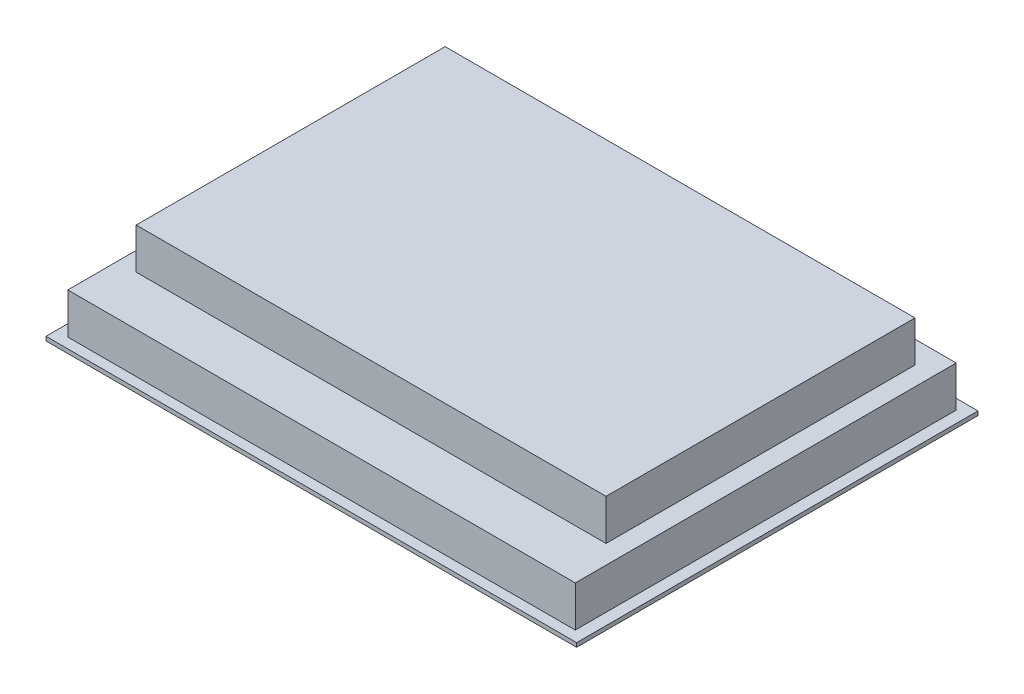
SolidWorks part; units mm, degrees
ref_plane "前视基准面" through (0, 0, 0) normal (0, 0, 1) x (1, 0, 0)
ref_plane "上视基准面" through (0, 0, 0) normal (0, 1, 0) x (1, 0, 0)
ref_plane "右视基准面" through (0, 0, 0) normal (1, 0, 0) x (0, 0, -1)
sketch "草图1" plane through (0, 0, 0) normal (0, 1, 0) x (1, 0, 0)
  line L1 (-195, -147.5) -> (195, -147.5)
  line L2 (-195, -147.5) -> (-195, 147.5)
  line L3 (-195, 147.5) -> (195, 147.5)
  line L4 (195, -147.5) -> (195, 147.5)
  line L5 (-195, -147.5) -> (195, 147.5) construction
  line L6 (-195, 147.5) -> (195, -147.5) construction
  point P0 (0, 0)
extrude "拉伸1" add sketch "草图1" along normal blind 3
sketch "草图2" plane through (0, 3, 0) normal (0, 1, 0) x (1, 0, 0)
  line L1 (-186.5, 140) -> (186.5, 140)
  line L2 (-186.5, 140) -> (-186.5, -140)
  line L3 (-186.5, -140) -> (186.5, -140)
  line L4 (186.5, 140) -> (186.5, -140)
  line L5 (-186.5, 140) -> (186.5, -140) construction
  line L6 (-186.5, -140) -> (186.5, 140) construction
  line L11 (-167.4114, -85.6768) -> (167.4114, 121.4193) construction
  line L12 (-167.4114, 121.4193) -> (167.4114, -85.6768) construction
  point P0 (0, 0)
  point P6 (0, 17.8712)
extrude "拉伸2" add sketch "草图2" along normal blind 30
sketch "草图4" plane through (0, 33, 0) normal (0, 1, 0) x (1, 0, 0)
  line L1 (-172.6676, 123.5217) -> (172.6676, 123.5217)
  line L2 (-172.6676, 123.5217) -> (-172.6676, -103.548)
  line L3 (-172.6676, -103.548) -> (172.6676, -103.548)
  line L4 (172.6676, 123.5217) -> (172.6676, -103.548)
  line L5 (-172.6676, 123.5217) -> (172.6676, -103.548) construction
  line L6 (-172.6676, -103.548) -> (172.6676, 123.5217) construction
  point P0 (0, 9.9869)
extrude "拉伸3" add sketch "草图4" along normal blind 30
sketch "草图5" plane through (0, 0, 0) normal (0, -1, 0) x (1, 0, 0)
  line L1 (195, 147.5) -> (195, -147.5) construction
  line L2 (195, -114.5) -> (152, -114.5)
  line L7 (-152, 114.5) -> (152, 114.5)
  line L8 (-152, 114.5) -> (-152, -114.5)
  line L9 (-152, -114.5) -> (152, -114.5)
  line L10 (152, 114.5) -> (152, -114.5)
extrude "拉伸4" cut sketch "草图5" against normal blind 2 contours L10 L7 L8 L9
